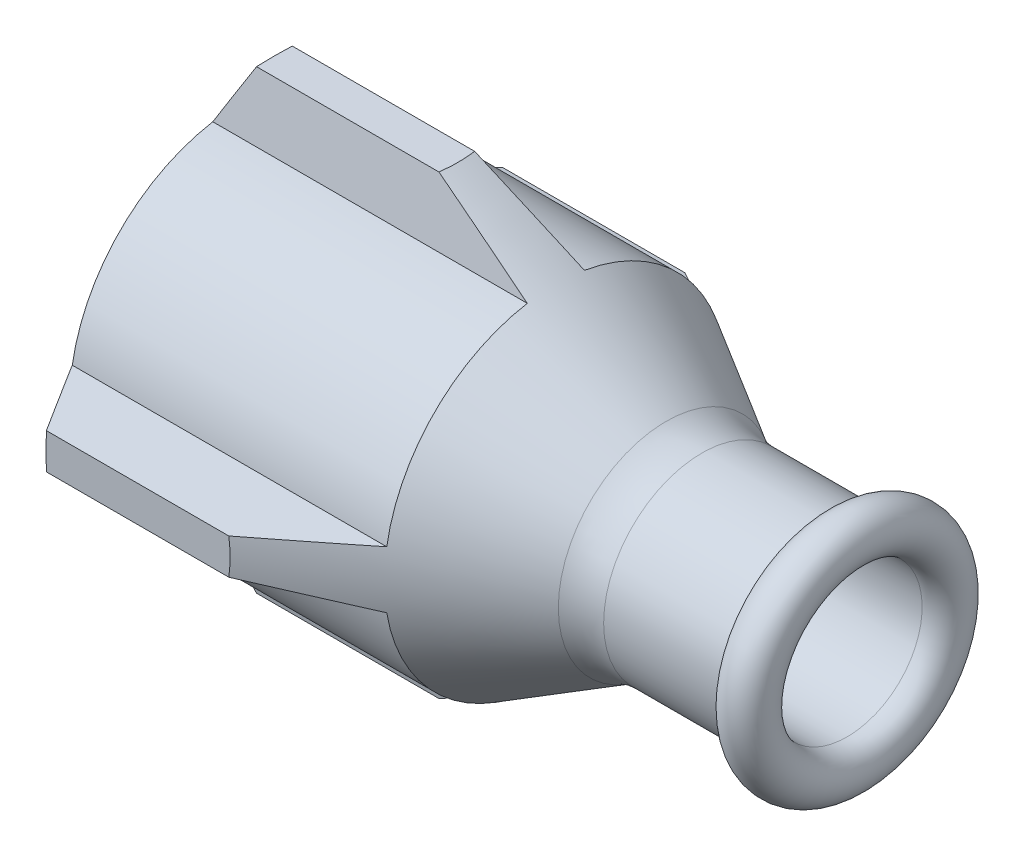
SolidWorks part; units mm, degrees
ref_plane "Front Plane" through (0, 0, 0) normal (0, 0, 1) x (1, 0, 0)
ref_plane "Top Plane" through (0, 0, 0) normal (0, 1, 0) x (1, 0, 0)
ref_plane "Right Plane" through (0, 0, 0) normal (1, 0, 0) x (0, 0, -1)
sketch "Sketch1" plane through (0, 0, 0) normal (0, 1, 0) x (1, 0, 0)
  line L0 (-40.5586, 0) -> (42.4318, 0) construction
  line L1 (0, 20.4829) -> (0, -20.4829) construction
  line L2 (0, 12) -> (0, 10.75)
  line L4 (0, 12) -> (22, 12)
  line L5 (3.5, 10.75) -> (0, 10.75)
  line L8 (18.5, 10.75) -> (20.5, 10.75)
  line L9 (20.5, 10.75) -> (24.5, 8.5)
  line L10 (24.5, 8.5) -> (26.5, 8.5)
  line L11 (26.5, 8.5) -> (26.5, 5.25)
  line L12 (26.5, 5.25) -> (42.375, 5.25)
  line L13 (0, 12) -> (44, 12) construction
  line L14 (18.5, 8.5) -> (44, 8.5) construction
  line L15 (22, 12) -> (28.0622, 8.5)
  line L16 (26.5, 6.875) -> (44, 6.875) construction
  line L17 (28.0622, 8.5) -> (29.7165, 7.5449)
  line L18 (32.2165, 6.875) -> (40.75, 6.875)
  line L19 (3.5, 10.75) -> (18.5, 10.75)
  line L20 (0, -21.4394) -> (0, 21.4394) construction
  arc A0 (42.375, 5.25) -> (40.75, 6.875) centre (42.375, 6.875) ccw
  arc A1 (29.7165, 7.5449) -> (32.2165, 6.875) centre (32.2165, 11.875) ccw
  point P27 (30.8768, 6.875)
  dimension "D16" = 5
  dimension "D1" = 12
  dimension "D2" = 10.75
  dimension "D3" = 3.5
  dimension "D4" = 15
  dimension "D5" = 44
  dimension "D6" = 2
  dimension "D7" = 10.75
  dimension "D8" = 2
  dimension "D9" = 4
  dimension "D10" = 8.5
  dimension "D11" = 5.25
  dimension "D12" = 22
  dimension "D13" = 30
  dimension "D14" = 1.625
  dimension "D15" = 1.625
  dimension "D17" = 5.25
  dimension "D18" = 26.5
revolve "Revolve1" add sketch "Sketch1" angle 360 about L0
sketch "Sketch5" plane through (0, 0, 0) normal (0, 0, 1) x (1, 0, 0)
  line L0 (22, -12) -> (15.0718, -16)
  line L1 (15.0718, -16) -> (2.3094, -16)
  line L2 (0, -21.4394) -> (0, 21.4394) construction
  line L4 (0, -12) -> (22, -12) construction
  line L5 (22, -12) -> (0, -12)
  line L6 (-0.8042, 0) -> (46.8758, 0) construction
  line L7 (0, -12) -> (2.3094, -16)
  line L8 (22, 12) -> (22, -12) construction
  point P14 (0, 0)
  point P15 (0, 0)
  dimension "D1" = 60
  dimension "D2" = 30
  dimension "D3" = 16
revolve "Revolve2" add sketch "Sketch5" angle 360 about L6
sketch "Sketch7" plane through (0, 0, 0) normal (1, 0, 0) x (0, 0, -1)
  line L0 (0, 16.0608) -> (0, 15.9511) construction
  line L1 (16.5965, 0) -> (15.9511, 0) construction
  line L2 (-15.9511, 1.25) -> (-15.9511, -1.25) construction
  line L4 (-11.8322, 2) -> (-15.9511, 1.25)
  line L5 (-15.9511, -1.25) -> (-11.8323, -1.9992)
  line L6 (-15.9511, 1.25) -> (-15.9511, -1.25)
  line L7 (1.25, 15.9511) -> (-1.25, 15.9511)
  line L8 (2, 11.8322) -> (1.25, 15.9511)
  line L10 (-1.25, 15.9511) -> (-1.9992, 11.8323)
  line L11 (15.9511, -1.25) -> (15.9511, 1.25)
  line L12 (11.8322, -2) -> (15.9511, -1.25)
  line L14 (15.9511, 1.25) -> (11.8323, 1.9992)
  line L15 (-1.25, -15.9511) -> (1.25, -15.9511)
  line L16 (-2, -11.8322) -> (-1.25, -15.9511)
  line L18 (1.25, -15.9511) -> (1.9992, -11.8323)
  line L19 (10.7356, 0) -> (-10.7356, 0) construction
  line L21 (0, 10.7356) -> (0, -10.7356) construction
  line L23 (-15.9511, 0) -> (-18.6227, 0) construction
  line L24 (0, -15.9511) -> (0, -16.5495) construction
  circle A0 centre (0, 0) radius 16
  arc A1 (11.8323, 1.9992) -> (2, 11.8322) centre (0, 0) ccw
  arc A2 (-1.9992, 11.8323) -> (-11.8322, 2) centre (0, 0) ccw
  arc A3 (-11.8323, -1.9992) -> (-2, -11.8322) centre (0, 0) ccw
  arc A4 (1.9992, -11.8323) -> (11.8322, -2) centre (0, 0) ccw
  point P11 (-16, 0)
  point P14 (-10.5476, 0)
  point P30 (0, 0)
  dimension "D6" = 32
  dimension "D7" = 12
  dimension "D1" = 2.5
  dimension "D2" = 1.25
  dimension "D3" = 2
  dimension "D8" = 3.9992
  dimension "D5" = 4
extrude "Cut-Extrude9" cut sketch "Sketch7" along normal through all contours L7 A0 | A3 L5 A0 L16 | A1 L14 A0 L8 | A2 L10 A0 L4 | A4 L18 A0 L12 | L15 A0 | L6 A0 | L11 A0
ref_plane "Plane1" through (0, 0, 0) normal (0, 0.7071, -0.7071) x (1, 0, 0)
ref_plane "Plane2" through (0, -8.4853, -8.4853) normal (0, 0.7071, 0.7071) x (1, 0, 0)
sketch "Sketch8" plane through (0, -8.4853, -8.4853) normal (0, 0.7071, 0.7071) x (1, 0, 0)
  line L0 (21.9622, 0) -> (0, 0) construction
  line L1 (6, 3.272) -> (6, -4.3274) construction
  line L2 (0, -21.4394) -> (0, 21.4394) construction
  circle A0 centre (6, 0) radius 1.5
  dimension "D1" = 6
extrude "Cut-Extrude10" cut sketch "Sketch8" along normal up to next
